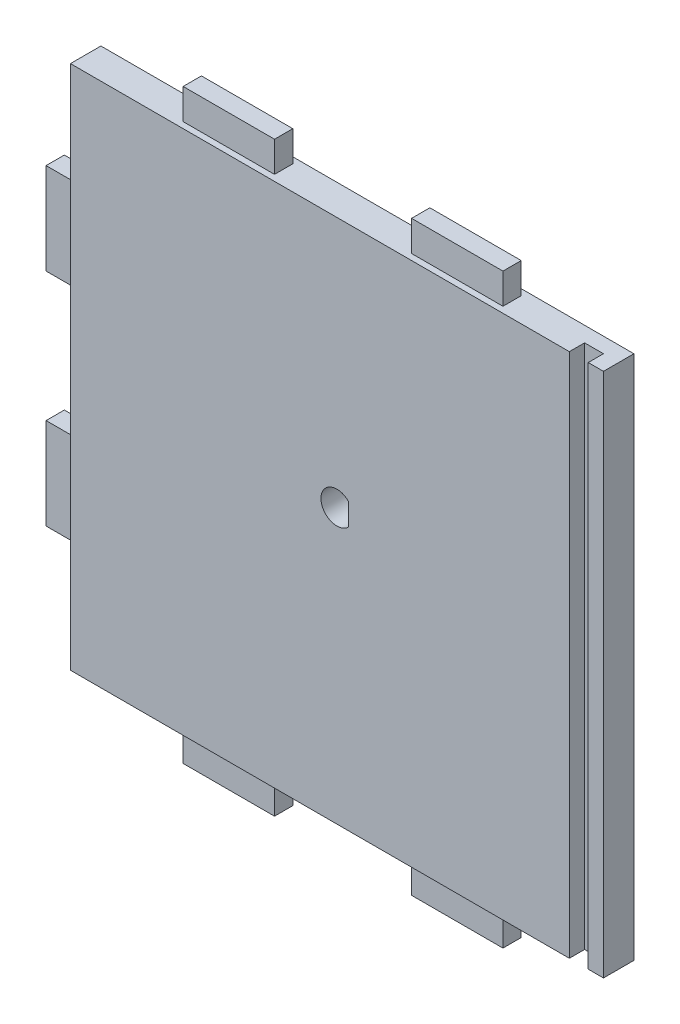
SolidWorks part; units mm, degrees
material "ABS"
ref_plane "Plano frontal" through (0, 0, 0) normal (0, 0, 1) x (1, 0, 0)
ref_plane "Plano superior" through (0, 0, 0) normal (0, 1, 0) x (1, 0, 0)
ref_plane "Plano direito" through (0, 0, 0) normal (1, 0, 0) x (0, 0, -1)
sketch "Esboço1" plane through (0, 0, 0) normal (0, 0, 1) x (1, 0, 0)
  line L1 (87.5, -86.25) -> (-87.5, -86.25)
  line L2 (87.5, -86.25) -> (87.5, 86.25)
  line L3 (87.5, 86.25) -> (-87.5, 86.25)
  line L4 (-87.5, -86.25) -> (-87.5, 86.25)
  line L5 (87.5, -86.25) -> (-87.5, 86.25) construction
  line L6 (87.5, 86.25) -> (-87.5, -86.25) construction
  point P0 (0, 0)
  dimension "D1" = 172.5
  dimension "D2" = 175
extrude "Ressalto-extrusão1" add sketch "Esboço1" along normal blind 10
sketch "Esboço5" plane through (0, 86.25, 0) normal (0, 1, 0) x (1, 0, 0)
  line L0 (0, 0) -> (0, -10) construction
  line L1 (87.5, -10) -> (-87.5, -10) construction
  line L2 (-87.5, -5) -> (87.5, -5) construction
  line L3 (-87.5, -10) -> (-87.5, 0) construction
  line L4 (87.5, -10) -> (87.5, 0) construction
  line L5 (22.5, -2) -> (52.5, -8) construction
  line L6 (-22.5, -8) -> (-52.5, -8)
  line L7 (-22.5, -8) -> (-22.5, -2)
  line L8 (-22.5, -2) -> (-52.5, -2)
  line L9 (-52.5, -8) -> (-52.5, -2)
  line L10 (-22.5, -8) -> (-52.5, -2) construction
  line L11 (-22.5, -2) -> (-52.5, -8) construction
  line L12 (22.5, -8) -> (52.5, -2) construction
  line L13 (52.5, -8) -> (52.5, -2)
  line L14 (22.5, -2) -> (52.5, -2)
  line L15 (22.5, -8) -> (22.5, -2)
  line L16 (22.5, -8) -> (52.5, -8)
  point P11 (-37.5, -5)
  point P20 (37.5, -5)
  dimension "D1" = 30
  dimension "D2" = 6
  dimension "D3" = 50
extrude "Ressalto-extrusão5" add sketch "Esboço5" along normal blind 10
sketch "Esboço6" plane through (-87.5, 0, 0) normal (-1, 0, 0) x (0, 0, 1)
  line L0 (5, 80.8371) -> (5, -100.2795) construction
  line L1 (0, 86.25) -> (0, -86.25) construction
  line L2 (-31.1105, 0) -> (49.0505, 0) construction
  line L3 (10, 86.25) -> (0, 86.25) construction
  line L4 (8, 21.25) -> (2, 21.25)
  line L5 (8, 21.25) -> (8, 51.25)
  line L6 (8, 51.25) -> (2, 51.25)
  line L7 (2, 21.25) -> (2, 51.25)
  line L8 (8, 21.25) -> (2, 51.25) construction
  line L9 (8, 51.25) -> (2, 21.25) construction
  line L10 (8, -51.25) -> (2, -21.25) construction
  line L11 (8, -21.25) -> (2, -51.25) construction
  line L12 (2, -21.25) -> (2, -51.25)
  line L13 (8, -51.25) -> (2, -51.25)
  line L14 (8, -21.25) -> (8, -51.25)
  line L15 (8, -21.25) -> (2, -21.25)
  point P6 (5, 36.25)
  point P19 (5, -36.25)
  dimension "D1" = 5
  dimension "D2" = 6
  dimension "D3" = 30
  dimension "D4" = 50
extrude "Ressalto-extrusão6" add sketch "Esboço6" along normal blind 10
sketch "Esboço7" plane through (0, -86.25, 0) normal (0, -1, 0) x (1, 0, 0)
  line L0 (-118.1326, 5) -> (111.1308, 5) construction
  line L1 (-87.5, 10) -> (87.5, 10) construction
  line L2 (0, -18.9857) -> (0, 24.411) construction
  line L3 (-87.5, 10) -> (-87.5, 0) construction
  line L4 (-22.5, 2) -> (-52.5, 2)
  line L5 (-22.5, 2) -> (-22.5, 8)
  line L6 (-22.5, 8) -> (-52.5, 8)
  line L7 (-52.5, 2) -> (-52.5, 8)
  line L8 (-22.5, 2) -> (-52.5, 8) construction
  line L9 (-22.5, 8) -> (-52.5, 2) construction
  line L10 (22.5, 8) -> (52.5, 2) construction
  line L11 (22.5, 2) -> (52.5, 8) construction
  line L12 (52.5, 2) -> (52.5, 8)
  line L13 (22.5, 8) -> (52.5, 8)
  line L14 (22.5, 2) -> (22.5, 8)
  line L15 (22.5, 2) -> (52.5, 2)
  point P6 (-37.5, 5)
  point P19 (37.5, 5)
  dimension "D1" = 5
  dimension "D2" = 30
  dimension "D3" = 6
  dimension "D4" = 50
extrude "Ressalto-extrusão7" add sketch "Esboço7" along normal blind 10
sketch "Esboço9" plane through (0, 0, 10) normal (0, 0, 1) x (1, 0, 0)
  line L0 (-128.9027, 0) -> (135.2115, 0) construction
  line L1 (87.5, 86.25) -> (-87.5, 86.25) construction
  line L2 (82.5, -86.25) -> (76.3, -86.25)
  line L3 (82.5, -86.25) -> (82.5, 86.25)
  line L4 (82.5, 86.25) -> (76.3, 86.25)
  line L5 (76.3, -86.25) -> (76.3, 86.25)
  line L6 (82.5, -86.25) -> (76.3, 86.25) construction
  line L7 (82.5, 86.25) -> (76.3, -86.25) construction
  line L8 (87.5, -86.25) -> (87.5, 86.25) construction
  point P2 (79.4, 0)
  dimension "D1" = 5
  dimension "D2" = 6.2
extrude "Corte-extrusão2" cut sketch "Esboço9" against normal blind 5
sketch "Esboço10" plane through (-87.5, 0, 0) normal (-1, 0, 0) x (0, 0, 1)
  line L0 (5, 90.017) -> (5, -99.8466) construction
  line L1 (0, 86.25) -> (0, -86.25) construction
  line L2 (10, -86.25) -> (0, -86.25) construction
  line L3 (-7.9793, -71.25) -> (19.2427, -71.25) construction
  circle A1 centre (5, -71.25) radius 1.5
  dimension "D2" = 3
  dimension "D3" = 15
  dimension "D1" = 5
extrude "Corte-extrusão3" cut sketch "Esboço10" against normal blind 8
sketch "Esboço11" plane through (0, -86.25, 0) normal (0, -1, 0) x (1, 0, 0)
  line L0 (-123.7293, 5) -> (109.1351, 5) construction
  line L1 (-87.5, 0) -> (87.5, 0) construction
  line L2 (87.5, 10) -> (87.5, 0) construction
  circle A0 centre (65, 5) radius 1.5
  dimension "D2" = 3
  dimension "D3" = 22.5
  dimension "D1" = 5
extrude "Corte-extrusão4" cut sketch "Esboço11" against normal blind 8
sketch "Esboço12" plane through (0, 0, 0) normal (0, 0, -1) x (-1, 0, 0)
  line L0 (-111.9518, 3.75) -> (111.9953, 3.75) construction
  line L1 (-87.5, 86.25) -> (87.5, 86.25) construction
  line L2 (0, 96.2682) -> (0, -105.7874) construction
  line L4 (-3.85, -1.25) -> (-6.65, -1.25)
  line L5 (-3.85, -1.25) -> (-3.85, 8.75)
  line L6 (-3.85, 8.75) -> (-6.65, 8.75)
  line L7 (-6.65, -1.25) -> (-6.65, 8.75)
  line L8 (-3.85, -1.25) -> (-6.65, 8.75) construction
  line L9 (-3.85, 8.75) -> (-6.65, -1.25) construction
  circle A0 centre (0, 3.75) radius 5.25
  point P11 (-5.25, 3.75)
  dimension "D2" = 10.5
  dimension "D1" = 82.5
  dimension "D3" = 10
  dimension "D4" = 2.8
extrude "Corte-extrusão5" cut sketch "Esboço12" against normal through all contours L5 A0
